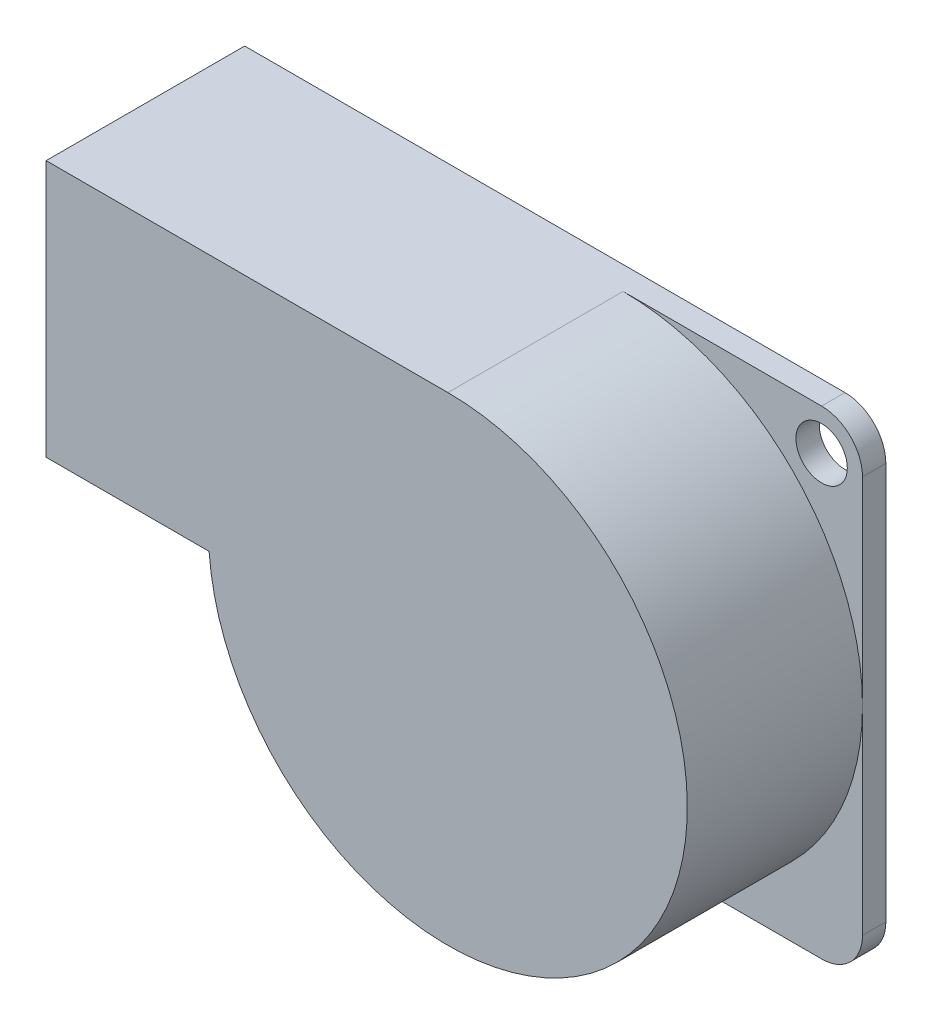
SolidWorks part; units mm, degrees
ref_plane "Front Plane" through (0, 0, 0) normal (0, 0, 1) x (1, 0, 0)
ref_plane "Top Plane" through (0, 0, 0) normal (0, 1, 0) x (1, 0, 0)
ref_plane "Right Plane" through (0, 0, 0) normal (1, 0, 0) x (0, 0, -1)
sketch "Sketch1" plane through (0, 0, 0) normal (0, 0, 1) x (1, 0, 0)
  line L0 (0, 1.75) -> (-25.7, 1.75)
  line L1 (-25.7, 1.75) -> (-25.7, -9.25)
  line L2 (-25.7, -9.25) -> (-18.75, -9.25)
  line L3 (-18.75, -9.25) -> (-18.75, -17)
  line L4 (-17, -18.75) -> (0, -18.75)
  line L5 (1.75, -17) -> (1.75, 0)
  circle A0 centre (0, 0) radius 1.1
  circle A1 centre (-17, -17) radius 1.1
  arc A2 (0, 1.75) -> (1.75, 0) centre (0, 0) cw
  arc A3 (0, -18.75) -> (1.75, -17) centre (0, -17) ccw
  arc A4 (-18.75, -17) -> (-17, -18.75) centre (-17, -17) ccw
  dimension "D2" = 2.2
  dimension "D10" = 1.75
  dimension "D1" = 25.7
  dimension "D3" = 17
  dimension "D4" = 17
  dimension "D5" = 20.5
  dimension "D6" = 1.75
  dimension "D7" = 1.75
  dimension "D8" = 1.75
  dimension "D9" = 11
extrude "Boss-Extrude1" add sketch "Sketch1" along normal blind 1
sketch "Sketch2" plane through (0, 0, 1) normal (0, 0, 1) x (1, 0, 0)
  line L0 (-25.7, -9.25) -> (-18.75, -9.25) construction
  line L1 (-25.7, 1.75) -> (-25.7, -9.25) construction
  line L2 (0, 1.75) -> (-25.7, 1.75) construction
  line L3 (-25.7, -9.25) -> (-18.7225, -9.25)
  line L4 (-25.7, 1.75) -> (-25.7, -9.25)
  line L5 (-8.5, 1.75) -> (-25.7, 1.75)
  line L6 (1.75, -17) -> (1.75, 0) construction
  line L7 (-17, -18.75) -> (0, -18.75) construction
  arc A0 (-18.7225, -9.25) -> (-8.5, 1.75) centre (-8.5, -8.5) ccw
extrude "Boss-Extrude2" add sketch "Sketch2" along normal offset from surface (7.5 mm away) 8.5 up to face at (1.1, 0, 0)
